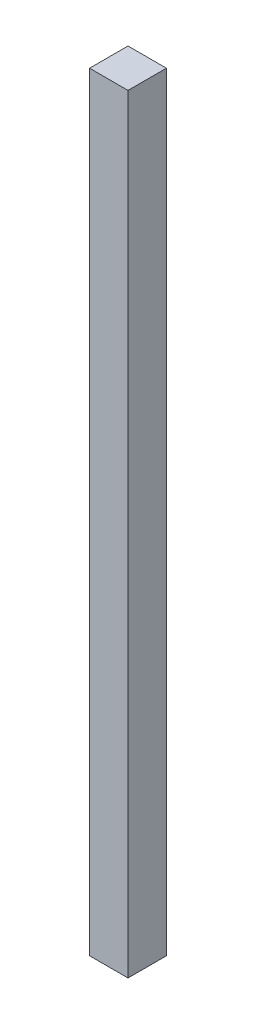
SolidWorks part; units mm, degrees
ref_plane "Front Plane" through (0, 0, 0) normal (0, 0, 1) x (1, 0, 0)
ref_plane "Top Plane" through (0, 0, 0) normal (0, 1, 0) x (1, 0, 0)
ref_plane "Right Plane" through (0, 0, 0) normal (1, 0, 0) x (0, 0, -1)
sketch "Sketch1" plane through (0, 0, 0) normal (0, 1, 0) x (1, 0, 0)
  line L1 (0, 0) -> (25.4, 0)
  line L2 (0, 0) -> (0, 25.4)
  line L3 (0, 25.4) -> (25.4, 25.4)
  line L4 (25.4, 0) -> (25.4, 25.4)
  dimension "D1" = 25.4
  dimension "D2" = 25.4
extrude "Boss-Extrude1" add sketch "Sketch1" along normal blind 508
